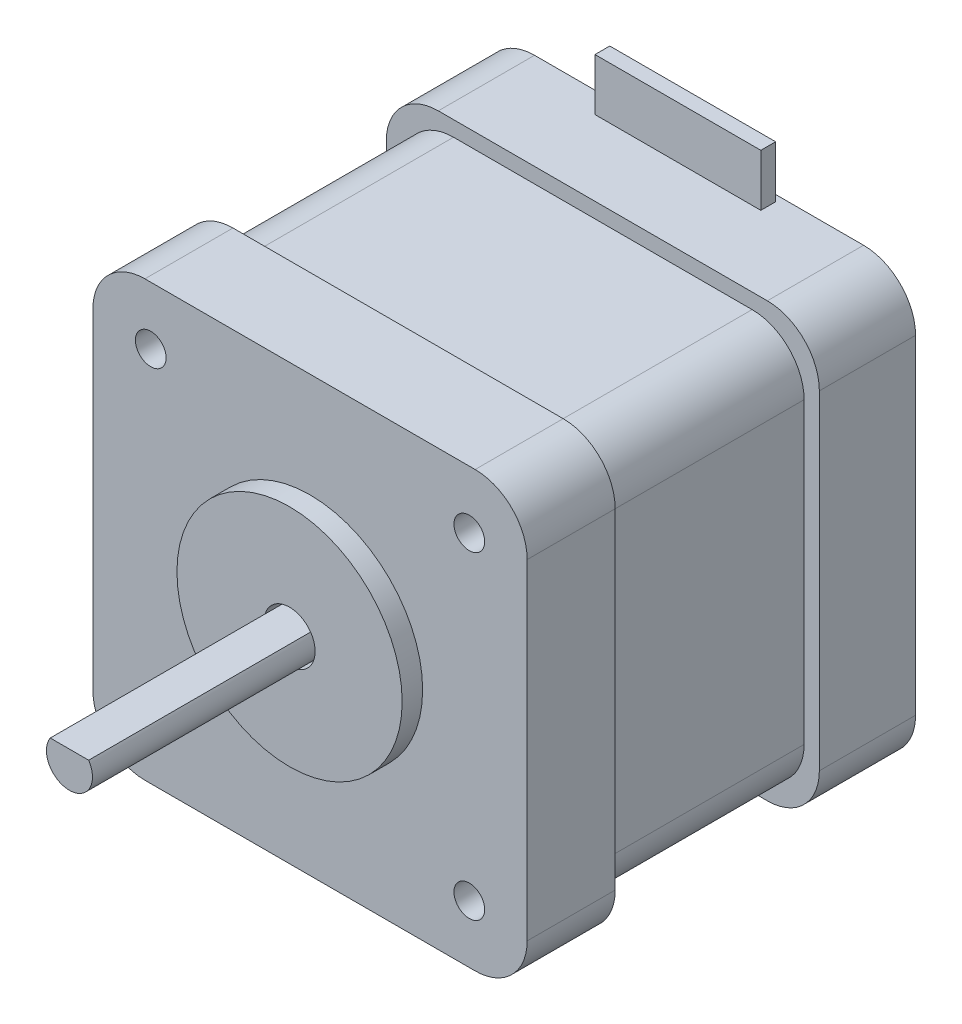
SolidWorks part; units mm, degrees
ref_plane "Front Plane" through (0, 0, 0) normal (0, 0, 1) x (1, 0, 0)
ref_plane "Top Plane" through (0, 0, 0) normal (0, 1, 0) x (1, 0, 0)
ref_plane "Right Plane" through (0, 0, 0) normal (1, 0, 0) x (0, 0, -1)
sketch "Sketch1" plane through (0, 0, 0) normal (0, 0, 1) x (1, 0, 0)
  line L1 (-16.07, -21.15) -> (16.07, -21.15)
  line L2 (-21.15, -16.07) -> (-21.15, 16.07)
  line L3 (-16.07, 21.15) -> (16.07, 21.15)
  line L4 (21.15, -16.07) -> (21.15, 16.07)
  line L5 (-21.15, -21.15) -> (21.15, 21.15) construction
  line L6 (-21.15, 21.15) -> (21.15, -21.15) construction
  arc A0 (-16.07, -21.15) -> (-21.15, -16.07) centre (-16.07, -16.07) cw
  arc A1 (16.07, -21.15) -> (21.15, -16.07) centre (16.07, -16.07) ccw
  arc A2 (16.07, 21.15) -> (21.15, 16.07) centre (16.07, 16.07) cw
  arc A3 (-21.15, 16.07) -> (-16.07, 21.15) centre (-16.07, 16.07) cw
  point P0 (0, 0)
  dimension "D3" = 5.08
  dimension "D1" = 42.3
  dimension "D2" = 42.3
extrude "Boss-Extrude1" add sketch "Sketch1" along normal blind 9.4
sketch "Sketch2" plane through (0, 0, 9.4) normal (0, 0, 1) x (1, 0, 0)
  line L1 (-14.5821, -19.6621) -> (14.5821, -19.6621)
  line L2 (-19.6621, -14.5821) -> (-19.6621, 14.5821)
  line L3 (-14.5821, 19.6621) -> (14.5821, 19.6621)
  line L4 (19.6621, -14.5821) -> (19.6621, 14.5821)
  line L5 (-19.6621, -19.6621) -> (19.6621, 19.6621) construction
  line L6 (-19.6621, 19.6621) -> (19.6621, -19.6621) construction
  arc A0 (21.15, 16.07) -> (16.07, 21.15) centre (16.07, 16.07) ccw construction
  arc A1 (14.5821, 19.6621) -> (19.6621, 14.5821) centre (14.5821, 14.5821) cw
  arc A2 (14.5821, -19.6621) -> (19.6621, -14.5821) centre (14.5821, -14.5821) ccw
  arc A3 (-14.5821, -19.6621) -> (-19.6621, -14.5821) centre (-14.5821, -14.5821) cw
  arc A4 (-19.6621, 14.5821) -> (-14.5821, 19.6621) centre (-14.5821, 14.5821) cw
  point P0 (0, 0)
  dimension "D1" = 5.08
extrude "Boss-Extrude2" add sketch "Sketch2" along normal blind 20
sketch "Sketch3" plane through (0, 0, 29.4) normal (0, 0, 1) x (1, 0, 0)
  line L1 (-14.5821, -19.6621) -> (14.5821, -19.6621)
  line L2 (-19.6621, -14.5821) -> (-19.6621, 14.5821)
  line L3 (-14.5821, 19.6621) -> (14.5821, 19.6621)
  line L4 (19.6621, -14.5821) -> (19.6621, 14.5821)
  line L5 (-19.6621, -19.6621) -> (19.6621, 19.6621) construction
  line L6 (-19.6621, 19.6621) -> (19.6621, -19.6621) construction
  arc A0 (14.5821, -19.6621) -> (19.6621, -14.5821) centre (14.5821, -14.5821) ccw
  arc A1 (-14.5821, -19.6621) -> (-19.6621, -14.5821) centre (-14.5821, -14.5821) cw
  arc A2 (14.5821, 19.6621) -> (19.6621, 14.5821) centre (14.5821, 14.5821) cw
  arc A3 (-19.6621, 14.5821) -> (-14.5821, 19.6621) centre (-14.5821, 14.5821) cw
  point P0 (0, 0)
  dimension "D1" = 5.08
sketch "Sketch4" plane through (0, 0, 29.4) normal (0, 0, 1) x (1, 0, 0)
  line L1 (16.129, -21.209) -> (-16.129, -21.209)
  line L2 (21.209, -16.129) -> (21.209, 16.129)
  line L3 (16.129, 21.209) -> (-16.129, 21.209)
  line L4 (-21.209, -16.129) -> (-21.209, 16.129)
  line L5 (21.209, -21.209) -> (-21.209, 21.209) construction
  line L6 (21.209, 21.209) -> (-21.209, -21.209) construction
  arc A0 (16.129, -21.209) -> (21.209, -16.129) centre (16.129, -16.129) ccw
  arc A1 (21.209, 16.129) -> (16.129, 21.209) centre (16.129, 16.129) ccw
  arc A2 (-16.129, 21.209) -> (-21.209, 16.129) centre (-16.129, 16.129) ccw
  arc A3 (-16.129, -21.209) -> (-21.209, -16.129) centre (-16.129, -16.129) cw
  point P0 (0, 0)
  dimension "D3" = 5.08
  dimension "D1" = 42.418
  dimension "D2" = 42.418
extrude "Boss-Extrude4" add sketch "Sketch4" along normal blind 8.6
sketch "Sketch5" plane through (0, 0, 38) normal (0, 0, 1) x (1, 0, 0)
  circle A0 centre (0, 0) radius 11
  dimension "D1" = 22
extrude "Boss-Extrude5" add sketch "Sketch5" along normal blind 2
sketch "Sketch6" plane through (0, 0, 40) normal (0, 0, 1) x (1, 0, 0)
  circle A0 centre (0, 0) radius 2.5
  dimension "D1" = 5
extrude "Cut-Extrude1" cut sketch "Sketch6" against normal blind 2
sketch "Sketch7" plane through (0, 0, 38) normal (0, 0, 1) x (1, 0, 0)
  line L0 (1.8761, 1.2421) -> (-1.8761, 1.2421)
  arc A0 (-1.8761, 1.2421) -> (1.8761, 1.2421) centre (0, 0) ccw
  dimension "D1" = 4.5
extrude "Boss-Extrude6" add sketch "Sketch7" along normal blind 23.5
sketch "Sketch8" plane through (0, 21.15, 0) normal (0, 1, 0) x (1, 0, 0)
  line L5 (16.07, 0) -> (-16.07, 0) construction
  line L6 (8.1, -0.6208) -> (-8.1, -0.6208)
  line L7 (8.1, -0.6208) -> (8.1, -2.0655)
  line L8 (8.1, -2.0655) -> (-8.1, -2.0655)
  line L9 (-8.1, -0.6208) -> (-8.1, -2.0655)
  line L10 (8.1, -0.6208) -> (-8.1, -2.0655) construction
  line L11 (8.1, -2.0655) -> (-8.1, -0.6208) construction
  point P0 (0, -1.3431)
  point P10 (0, 0)
  dimension "D1" = 16.2
  dimension "D2" = 0
  dimension "D3" = 1.4446
extrude "Boss-Extrude7" add sketch "Sketch8" along normal blind 5.08
sketch "Sketch9" plane through (0, 0, 38) normal (0, 0, 1) x (1, 0, 0)
  line L1 (-16.129, -21.209) -> (16.129, -21.209) construction
  line L2 (-21.209, 16.129) -> (-21.209, -16.129) construction
  line L5 (21.209, -16.129) -> (21.209, 16.129) construction
  line L6 (16.129, 21.209) -> (-16.129, 21.209) construction
  circle A0 centre (-15.559, 15.559) radius 1.5
  circle A1 centre (15.559, 15.559) radius 1.5
  circle A2 centre (15.559, -15.559) radius 1.5
  circle A3 centre (-15.559, -15.559) radius 1.5
  point P0 (0, 0)
  dimension "D3" = 3
  dimension "D4" = 3
  dimension "D5" = 3
  dimension "D6" = 3
  dimension "D2" = 5.65
  dimension "D7" = 5.65
  dimension "D8" = 5.65
  dimension "D9" = 5.65
  dimension "D10" = 5.65
  dimension "D11" = 5.65
  dimension "D12" = 5.65
  dimension "D13" = 5.65
extrude "Cut-Extrude2" cut sketch "Sketch9" against normal blind 4.5
